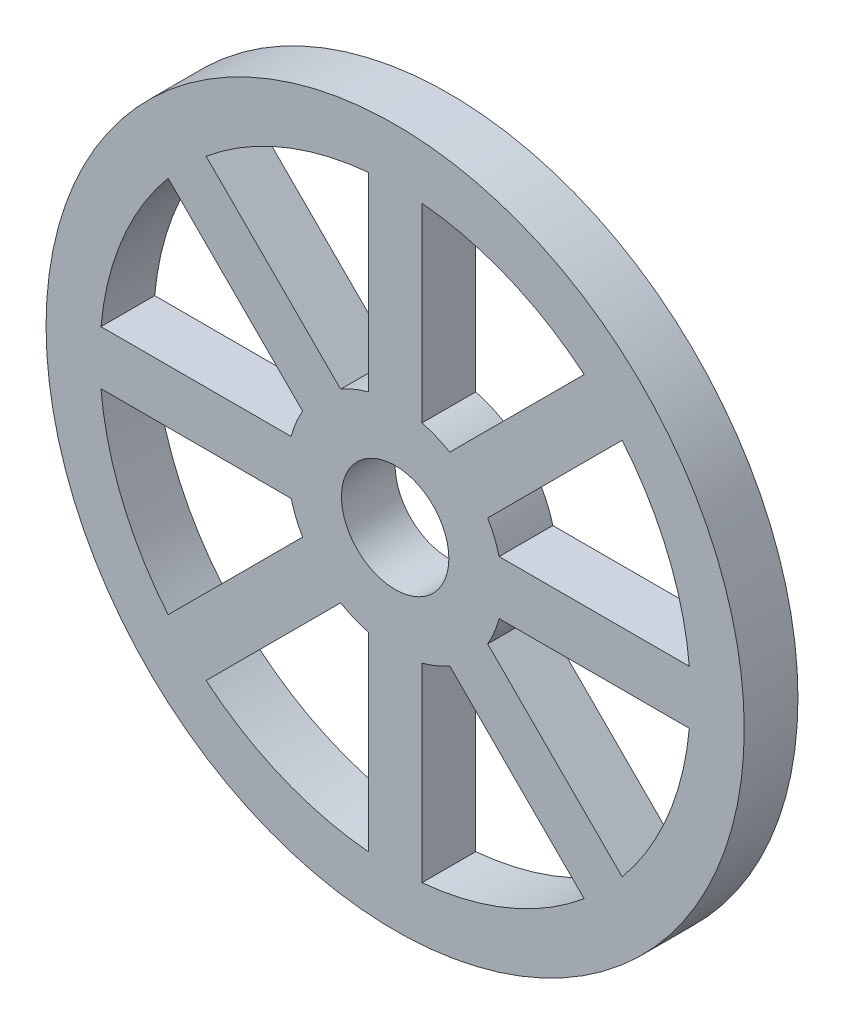
SolidWorks part; units mm, degrees
ref_plane "Ebene vorne" through (0, 0, 0) normal (0, 0, 1) x (1, 0, 0)
ref_plane "Ebene oben" through (0, 0, 0) normal (0, 1, 0) x (1, 0, 0)
ref_plane "Ebene rechts" through (0, 0, 0) normal (1, 0, 0) x (0, 0, -1)
sketch "Skizze1" plane through (0, 0, 0) normal (0, 0, 1) x (1, 0, 0)
  circle A0 centre (0, 0) radius 32.5
  circle A1 centre (0, 0) radius 5
  dimension "D1" = 65
  dimension "D2" = 10
extrude "Aufsatz-Linear austragen1" add sketch "Skizze1" against normal blind 5
sketch "Skizze2" plane through (0, 0, 0) normal (0, 0, 1) x (1, 0, 0)
  line L0 (0, 0) -> (0, 34.7276) construction
  line L1 (0, 0) -> (25.8307, 25.8307) construction
  line L2 (2.5, 27.3861) -> (2.5, 9.6825)
  line L3 (17.5971, 21.1327) -> (5.0788, 8.6143)
  circle A3 centre (0, 0) radius 27.5
  arc A4 (17.5971, 21.1327) -> (2.5, 27.3861) centre (0, 0) ccw
  circle A6 centre (0, 0) radius 10
  arc A7 (5.0788, 8.6143) -> (2.5, 9.6825) centre (0, 0) ccw
  dimension "D1" = 45
  dimension "D4" = 5
  dimension "D5" = 5
  dimension "D2" = 5
  dimension "D3" = 5
extrude "Schnitt-Linear austragen1" cut sketch "Skizze2" against normal through all
pattern_circular "Kreismuster1" count 8 over 360 about axis through (0, 0, 0) along (0, 0, 1) of "Schnitt-Linear austragen1"
